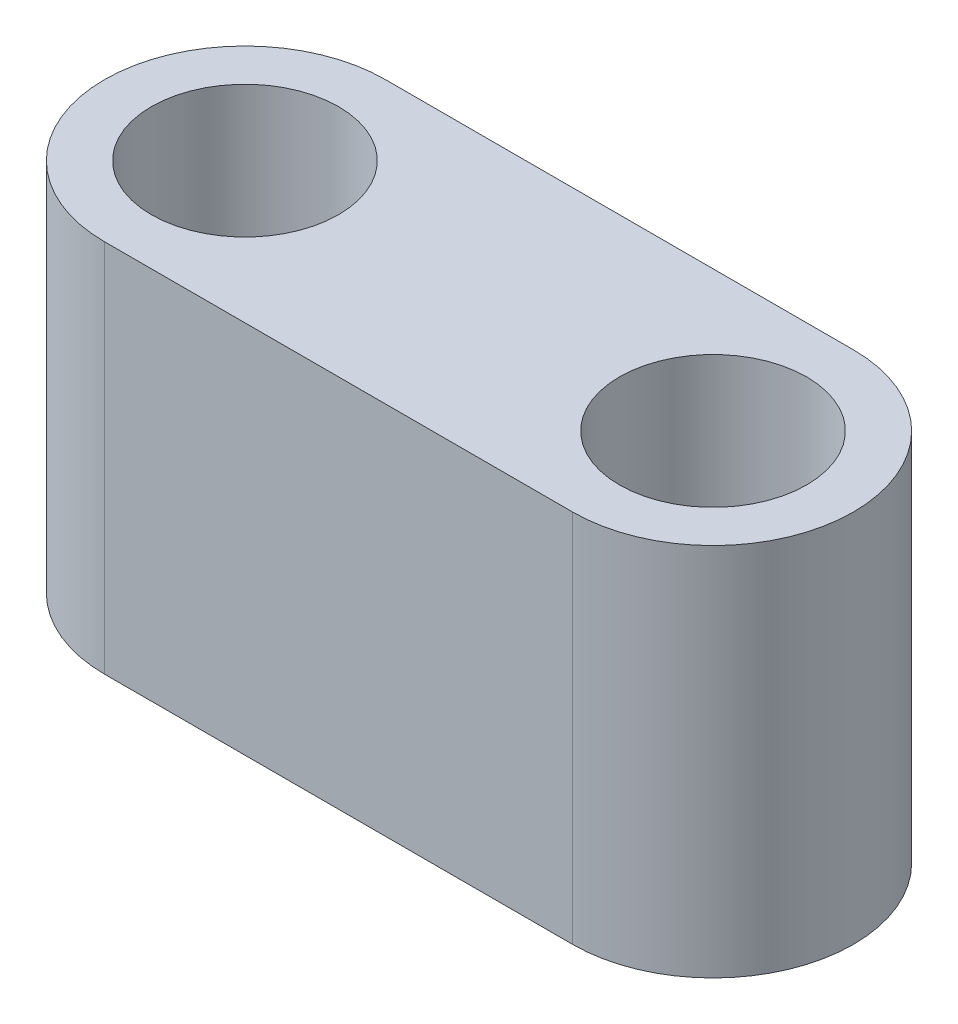
SolidWorks part; units mm, degrees
ref_plane "Front Plane" through (0, 0, 0) normal (0, 0, 1) x (1, 0, 0)
ref_plane "Top Plane" through (0, 0, 0) normal (0, 1, 0) x (1, 0, 0)
ref_plane "Right Plane" through (0, 0, 0) normal (1, 0, 0) x (0, 0, -1)
sketch "Sketch1" plane through (0, 0, 0) normal (0, 1, 0) x (1, 0, 0)
  line L0 (0, 0) -> (5, 0) construction
  line L1 (0, 1.5) -> (5, 1.5)
  line L2 (0, -1.5) -> (5, -1.5)
  arc A0 (0, 1.5) -> (0, -1.5) centre (0, 0) ccw
  arc A1 (5, -1.5) -> (5, 1.5) centre (5, 0) ccw
  circle A2 centre (0, 0) radius 1
  circle A3 centre (5, 0) radius 1
  point P3 (2.5, 0)
  dimension "D1" = 1.5
  dimension "D2" = 2
  dimension "D3" = 5
extrude "Boss-Extrude1" add sketch "Sketch1" along normal blind 4
